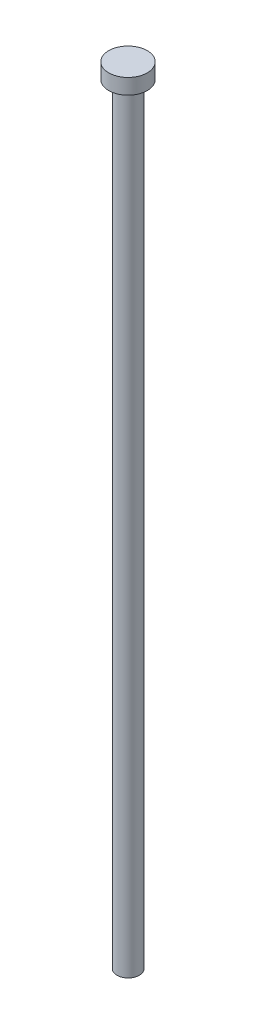
SolidWorks part; units mm, degrees
ref_plane "Front Plane" through (0, 0, 0) normal (0, 0, 1) x (1, 0, 0)
ref_plane "Top Plane" through (0, 0, 0) normal (0, 1, 0) x (1, 0, 0)
ref_plane "Right Plane" through (0, 0, 0) normal (1, 0, 0) x (0, 0, -1)
sketch "Sketch1" plane through (0, 0, 0) normal (0, 1, 0) x (1, 0, 0)
  circle A0 centre (-0.0217, 0.0463) radius 1.45
  dimension "D1" = 2.9
extrude "Boss-Extrude1" add sketch "Sketch1" along normal blind 100
sketch "Sketch2" plane through (0, 0, 0) normal (0, -1, 0) x (1, 0, 0)
  circle A0 centre (-0.0003, 0.0001) radius 2.5
  dimension "D1" = 5
sketch "Sketch3" plane through (0, 100, 0) normal (0, 1, 0) x (1, 0, 0)
  circle A0 centre (0.0107, -0.0063) radius 2.5
  dimension "D1" = 5
extrude "Boss-Extrude3" add sketch "Sketch3" along normal blind 2
